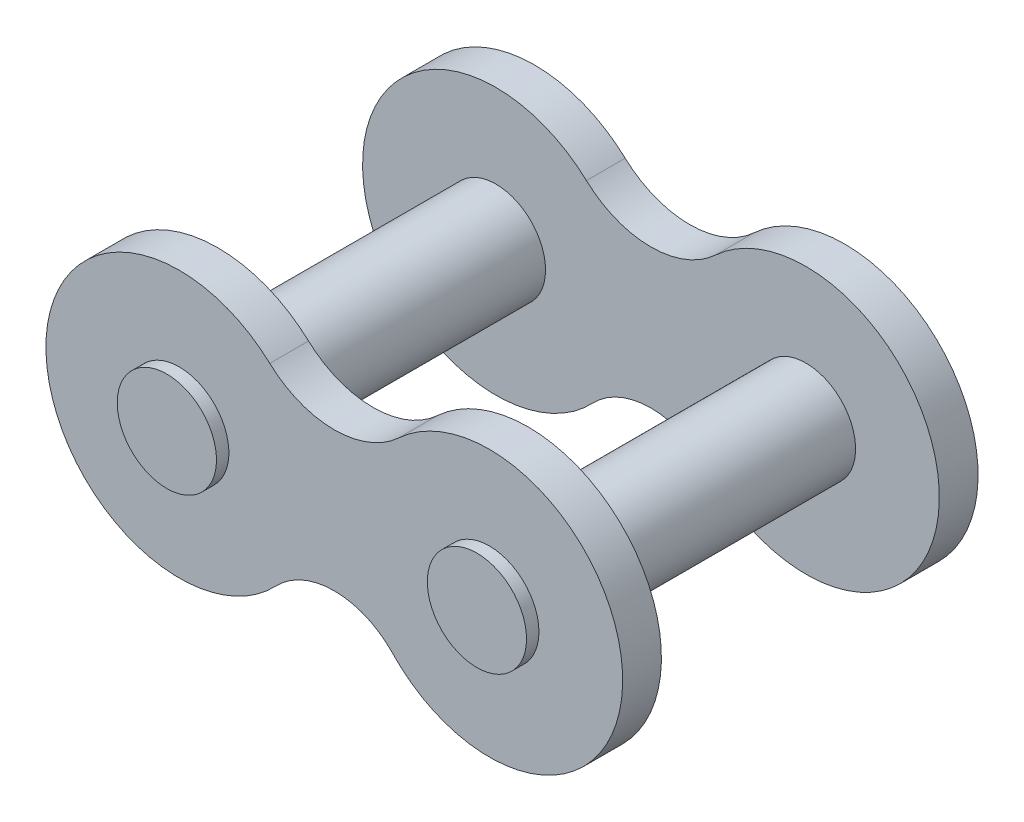
SolidWorks part; units mm, degrees
ref_plane "Front Plane" through (0, 0, 0) normal (0, 0, 1) x (1, 0, 0)
ref_plane "Top Plane" through (0, 0, 0) normal (0, 1, 0) x (1, 0, 0)
ref_plane "Right Plane" through (0, 0, 0) normal (1, 0, 0) x (0, 0, -1)
sketch "Sketch1" plane through (0, 0, 0) normal (0, 0, 1) x (1, 0, 0)
  line L0 (-40.2067, 0) -> (40.6277, 0) construction
  line L1 (0, -28.2078) -> (0, 34.102) construction
  circle A0 centre (-6.35, 0) radius 2.032
  arc A1 (-2.6422, 4.0093) -> (-2.3926, -3.7632) centre (-6.35, 0) ccw
  circle A2 centre (6.35, 0) radius 2.032
  arc A3 (2.6422, 4.0093) -> (2.3926, -3.7632) centre (6.35, 0) cw
  arc A4 (-2.6422, 4.0093) -> (2.6422, 4.0093) centre (0, 6.8664) ccw
  arc A5 (-2.3926, -3.7632) -> (2.3926, -3.7632) centre (0, -6.0384) cw
  dimension "D1" = 4.064
  dimension "D2" = 10.922
  dimension "D4" = 3.3017
  dimension "D5" = 3.8916
  dimension "D3" = 6.35
extrude "Boss-Extrude1" add sketch "Sketch1" along normal blind 1.5875
sketch "Sketch2" plane through (0, 0, 0) normal (0, 0, -1) x (-1, 0, 0)
  circle A0 centre (6.35, 0) radius 2.032 construction
  circle A1 centre (6.35, 0) radius 2.032
extrude "Boss-Extrude2" add sketch "Sketch2" against normal blind 15.0652 and the other way blind 0.508
ref_plane "Plane2" through (0, 0, 7.2786) normal (0, 0, -1) x (-1, 0, 0)
mirror "Mirror2" about plane through (0, 0, 7.2786) normal (0, 0, -1) of "Boss-Extrude1"
mirror "Mirror3" about plane through (0, 0, 0) normal (1, 0, 0) of "Boss-Extrude2"
ref_plane "Plane3" through (0, 0, 7.2786) normal (0, 0, -1) x (-1, 0, 0)
